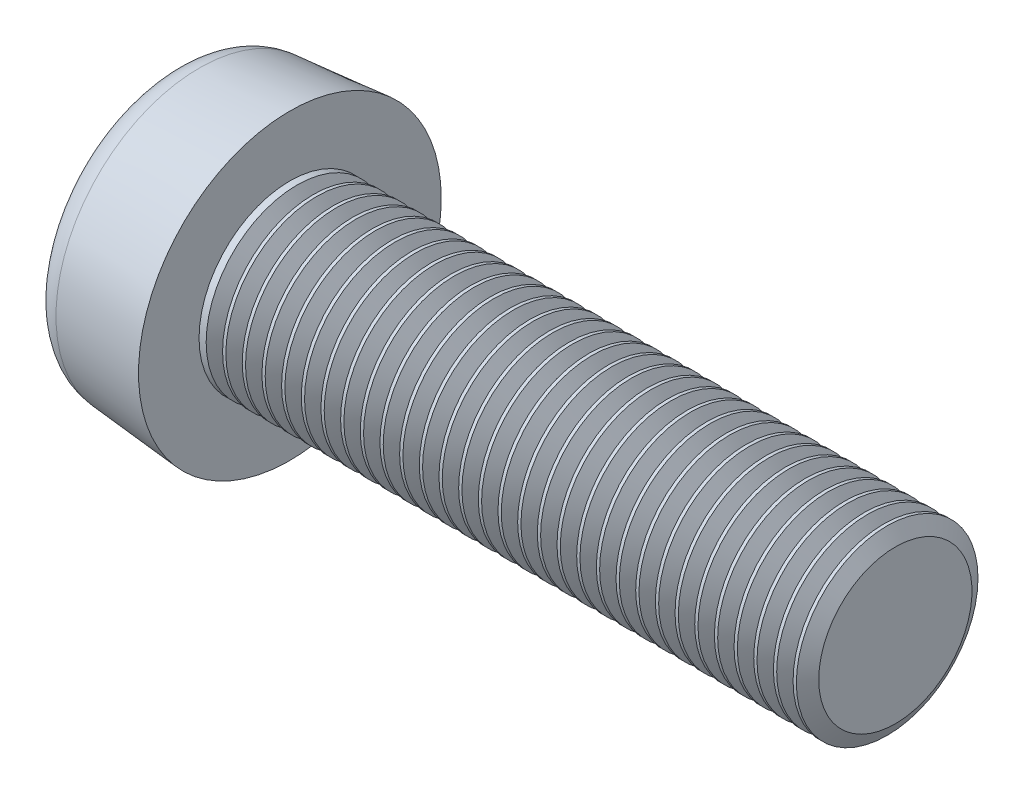
SolidWorks part; units mm, degrees
ref_plane "Front" through (0, 0, 0) normal (0, 0, 1) x (1, 0, 0)
ref_plane "Top" through (0, 0, 0) normal (0, 1, 0) x (1, 0, 0)
ref_plane "Right" through (0, 0, 0) normal (1, 0, 0) x (0, 0, -1)
ref_plane "Plane1" through (3.9, 0, 0) normal (1, 0, 0) x (0, 0, -1)
sketch "Sketch1" plane through (3.9, 0, 0) normal (1, 0, 0) x (0, 0, -1)
  circle A0 centre (0, 0) radius 5
  dimension "dk" = 10
extrude "BaseHead" add sketch "Sketch1" against normal blind 3.9 draft 5
sketch "Sketch2" plane through (3.9, 0, 0) normal (1, 0, 0) x (0, 0, -1)
  circle A0 centre (0, 0) radius 3
sketch "Sketch8" plane through (0, 0, 0) normal (0, 0, 1) x (1, 0, 0)
  line L0 (0, 0) -> (35.73, 0) construction
  line L1 (6.964, 0) -> (6.964, -2) construction
  line L2 (3.9, -5) -> (3.9, 5) construction
  line L3 (11.6578, 0) -> (11.6578, -5.35) construction
  line L4 (3.9, 3) -> (23.9, 3)
  line L5 (23.9, 3) -> (23.9, 0)
  line L7 (23.9, 0) -> (3.9, 0)
  line L9 (3.9, 3) -> (3.9, 0)
  arc A0 (6.7996, -0.1884) -> (7.1407, -0.1768) centre (6.964, 0) ccw construction
  dimension "r" = 0.25
  dimension "a" = 2
  dimension "d" = 6
  dimension "D4" = 5.35
  dimension "l" = 20
revolve "Revolve1" add sketch "Sketch8" angle 360 about L0
cosmetic thread "ThreadCosmetic1" [suppressed] parameters "bb"=20, "THD_MINOR"=4.917
sketch "Sketch4" plane through (0, 0, 0) normal (1, 0, 0) x (0, 0, -1)
  line L1 (0, 2.396) -> (-2.075, 1.198) construction
  line L2 (-2.075, 1.198) -> (-2.075, -1.198) construction
  line L3 (-2.075, -1.198) -> (0, -2.396) construction
  line L4 (0, -2.396) -> (2.075, -1.198) construction
  line L5 (2.075, -1.198) -> (2.075, 1.198) construction
  line L6 (2.075, 1.198) -> (0, 2.396) construction
  line L7 (1.0375, 1.797) -> (-1.0375, 1.797) construction
  line L8 (-1.0375, 1.797) -> (-2.075, 0) construction
  line L9 (-2.075, 0) -> (-1.0375, -1.797) construction
  line L10 (-1.0375, -1.797) -> (1.0375, -1.797) construction
  line L11 (1.0375, -1.797) -> (2.075, 0) construction
  line L12 (2.075, 0) -> (1.0375, 1.797) construction
  circle A0 centre (0, 0) radius 2.396 construction
  circle A1 centre (0, 0) radius 2.075 construction
  spline S0 degree 3 poles (0, 2.7646) (0.9577, 1.6588) (2.3942, 1.3823) (1.9154, 0) (2.3942, -1.3823) (0.9577, -1.6588) (0, -2.7646) (-0.9577, -1.6588) (-2.3942, -1.3823) (-1.9154, 0) (-2.3942, 1.3823) (-0.9577, 1.6588) (0, 2.7646) (0.9577, 1.6588) (2.3942, 1.3823) knots -0.25 -0.166667 -0.083333 0 0.083333 0.166667 0.25 0.333333 0.416667 0.5 0.583333 0.666667 0.75 0.833333 0.916667 1 1.083333 1.166667 1.25 only from (1.0375, 1.797) to (1.0375, 1.797)
  dimension "B" = 4.15
extrude "Socket" cut sketch "Sketch4" along normal blind 2
sketch "Sketch5" plane through (2, 0, 0) normal (-1, 0, 0) x (0, 0, 1)
  spline S1 degree 3 poles (0, 2.7646) (-0.9577, 1.6588) (-2.3942, 1.3823) (-1.9154, 0) (-2.3942, -1.3823) (-0.9577, -1.6588) (0, -2.7646) (0.9577, -1.6588) (2.3942, -1.3823) (1.9154, 0) (2.3942, 1.3823) (0.9577, 1.6588) (0, 2.7646) (-0.9577, 1.6588) (-2.3942, 1.3823) knots -0.25 -0.166667 -0.083333 0 0.083333 0.166667 0.25 0.333333 0.416667 0.5 0.583333 0.666667 0.75 0.833333 0.916667 1 1.083333 1.166667 1.25 only from (-1.0375, 1.797) to (-1.0375, 1.797)
  spline S2 degree 3 poles (0, 2.7646) (-0.9577, 1.6588) (-2.3942, 1.3823) (-1.9154, 0) (-2.3942, -1.3823) (-0.9577, -1.6588) (0, -2.7646) (0.9577, -1.6588) (2.3942, -1.3823) (1.9154, 0) (2.3942, 1.3823) (0.9577, 1.6588) (0, 2.7646) (-0.9577, 1.6588) (-2.3942, 1.3823) knots -0.25 -0.166667 -0.083333 0 0.083333 0.166667 0.25 0.333333 0.416667 0.5 0.583333 0.666667 0.75 0.833333 0.916667 1 1.083333 1.166667 1.25 only from (-1.0375, 1.797) to (-1.0375, 1.797)
  dimension "D1" = 0
ref_plane "Plane2" through (2.6667, 0, 0) normal (-1, 0, 0) x (0, 0, 1)
sketch "Sketch7" plane through (2.6667, 0, 0) normal (-1, 0, 0) x (0, 0, 1)
  point P0 (0, 0)
loft "Cut-Loft1" cut profiles "Sketch7", "Sketch5"
sketch "Sketch6" plane through (-30.7487, 13.2487, 0) normal (0, 0, 1) x (0, -1, 0)
  line L0 (13.2487, 89.8637) -> (13.2487, 24.8312) construction
  line L1 (-4.2098, 34.6487) -> (10.6902, 34.6487)
  line L2 (-4.2098, 34.6487) -> (-4.2098, 16.6487)
  line L3 (-4.2098, 16.6487) -> (10.2487, 16.6487)
  line L4 (10.7902, 34.7487) -> (10.7902, 14.1487)
  line L5 (16.2487, 54.6487) -> (10.2487, 54.6487) construction
  line L6 (10.2487, 16.6487) -> (10.7902, 14.1487)
  line L9 (18.2487, 34.6487) -> (8.2487, 34.6487) construction
  arc A0 (10.6902, 34.6487) -> (10.7902, 34.7487) centre (10.6902, 34.7487) ccw
  dimension "d1" = 4.917
  dimension "D2" = 15
  dimension "b" = 38
  dimension "D3" = 6
  dimension "x" = 2.5
fillet "HeadFillet2" radius 1 1 edges at (0, 0, -4.6588)
sketch "Sketch9" plane through (0, 0, 0) normal (0, 0, 1) x (1, 0, 0)
  line L0 (23.9, 2.531) -> (24.1708, 3)
  line L1 (24.1708, 3) -> (24.1708, 3.5415)
  line L2 (24.1708, 3.5415) -> (23.6293, 3.5415)
  line L3 (23.6293, 3.5415) -> (23.6293, 3)
  line L4 (23.6293, 3) -> (23.9, 2.531)
  line L5 (23.9, -3) -> (23.9, 3) construction
  line L6 (0, 0) -> (28.2938, 0) construction
  line L7 (0, 3.7425) -> (0, -3.7425) construction
  dimension "D1" = 0.5415
  dimension "D2" = 6
revolve "Cut-Revolve10" cut sketch "Sketch9" angle 360 about L6
pattern_linear "LPattern10" count 31 spacing 0.6498 along (-1, 0, 0) of "Cut-Revolve10"
equation "\"D1@Plane1\"=\"k@BaseHead\""
equation "\"D1@Plane2\" = \"t@Socket\" / 3"
equation "\"D2@Sketch9\" =\"d@Sketch8\""
equation "\"D1@Sketch9\" =  ( \"d@Sketch8\" - \"THD_MINOR@ThreadCosmetic1\" )  / 2"
equation "\"D3@LPattern10\" = \"D1@Sketch9\" * 1.2"
equation "\"D1@LPattern10\" = \"bb@ThreadCosmetic1\" / \"D3@LPattern10\" "
equation "\"D3@Sketch6\" = \"d@Sketch8\""
